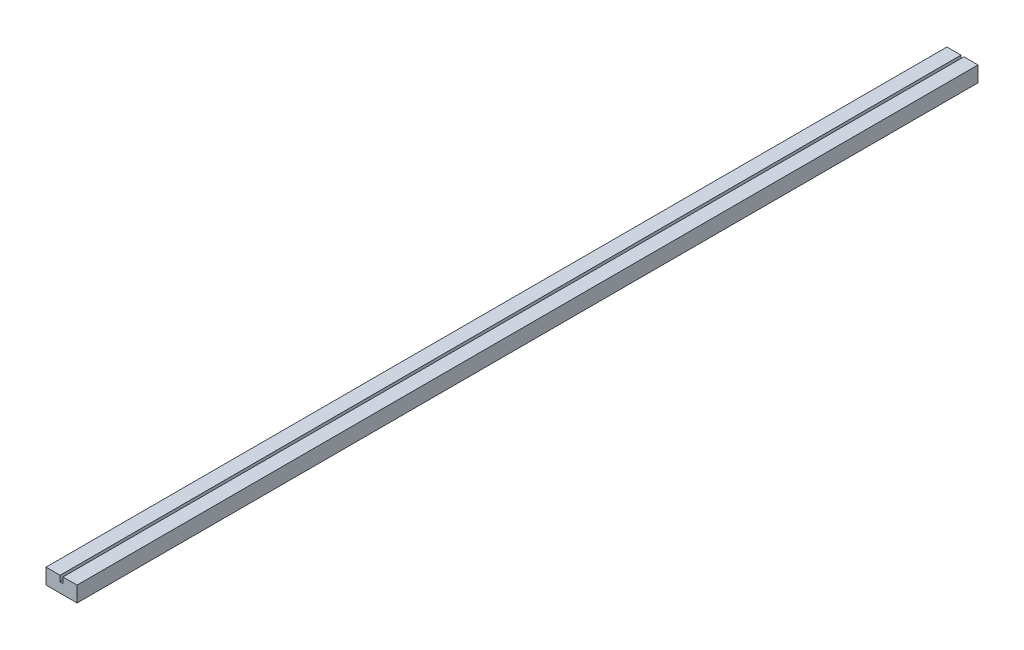
SolidWorks part; units mm, degrees
material "Pine"
ref_plane "Front Plane" through (0, 0, 0) normal (0, 0, 1) x (1, 0, 0)
ref_plane "Top Plane" through (0, 0, 0) normal (0, 1, 0) x (1, 0, 0)
ref_plane "Right Plane" through (0, 0, 0) normal (1, 0, 0) x (0, 0, -1)
sketch "Sketch1" plane through (0, 0, 0) normal (0, 0, 1) x (1, 0, 0)
  line L0 (0, 0) -> (0, 50.8)
  line L1 (0, 50.8) -> (101.6, 50.8)
  line L2 (101.6, 50.8) -> (101.6, 0)
  line L3 (101.6, 0) -> (0, 0)
  dimension "D1" = 50.8
  dimension "D2" = 101.6
extrude "Boss-Extrude1" add sketch "Sketch1" along normal blind 2946.4
sketch "Sketch2" plane through (0, 50.8, 0) normal (0, 1, 0) x (1, 0, 0)
  line L0 (50.8, -2946.4) -> (46.0375, -2946.4)
  line L1 (101.6, -2946.4) -> (0, -2946.4) construction
  line L2 (50.8, -2946.4) -> (55.5625, -2946.4)
  line L3 (46.0375, -2946.4) -> (46.0375, 0)
  line L4 (101.6, 0) -> (0, 0) construction
  line L5 (46.0375, 0) -> (55.5625, 0)
  line L6 (55.5625, 0) -> (55.5625, -2946.4)
  dimension "D1" = 4.7625
  dimension "D2" = 4.7625
extrude "Cut-Extrude1" cut sketch "Sketch2" against normal blind 19.05
